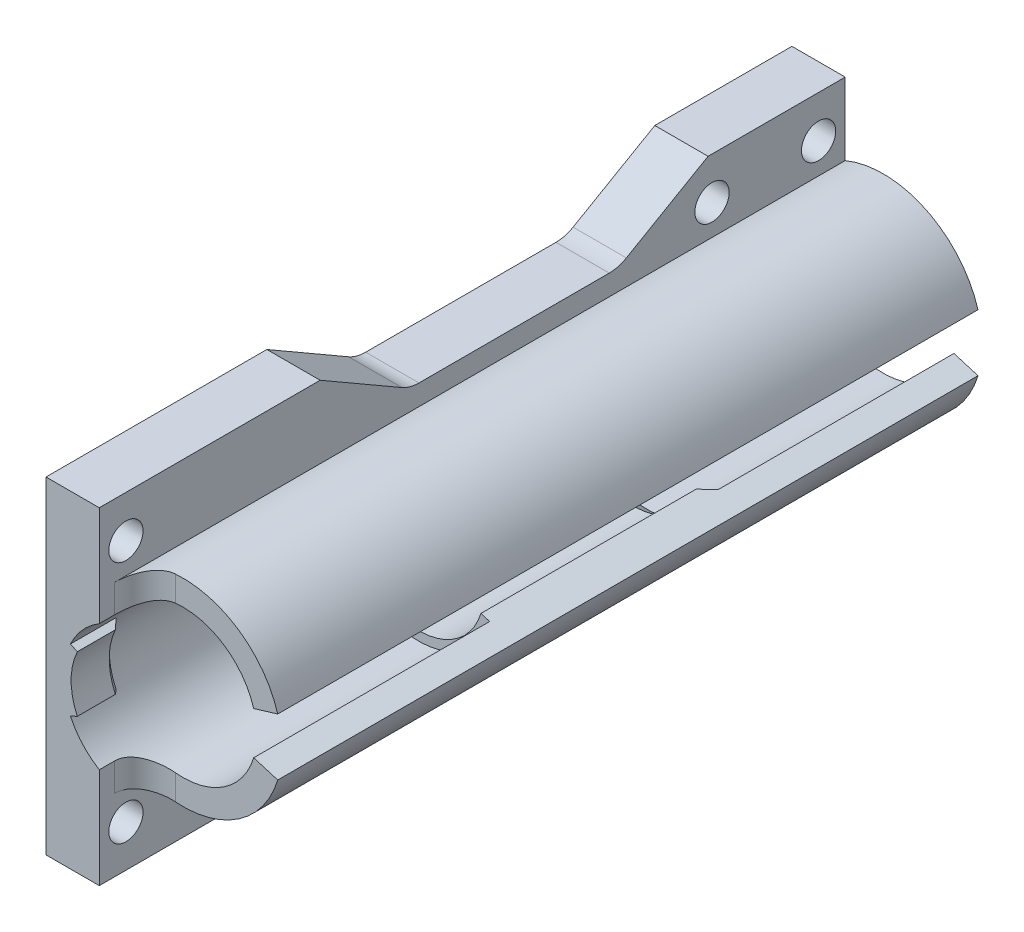
SolidWorks part; units mm, degrees
ref_plane "Front Plane" through (0, 0, 0) normal (0, 0, 1) x (1, 0, 0)
ref_plane "Top Plane" through (0, 0, 0) normal (0, 1, 0) x (1, 0, 0)
ref_plane "Right Plane" through (0, 0, 0) normal (1, 0, 0) x (0, 0, -1)
sketch "Sketch1" plane through (0, 0, 0) normal (0, 0, 1) x (1, 0, 0)
  line L0 (-5, -12) -> (-5, -21.5)
  line L1 (-12, 21.5) -> (-5, 21.5)
  line L2 (-12, 21.5) -> (-12, -21.5)
  line L3 (-12, -21.5) -> (-5, -21.5)
  line L4 (-5, 21.5) -> (-5, 12)
  line L5 (-12, 0) -> (0, 0) construction
  line L6 (9.2871, 2.8) -> (12.4466, 3.7526)
  line L7 (9.2871, -2.8) -> (12.4466, -3.7526)
  arc A0 (9.2871, 2.8) -> (9.2871, -2.8) centre (0, 0) ccw
  arc A1 (-5, -12) -> (12.4466, -3.7526) centre (0, 0) ccw
  arc A2 (12.4466, 3.7526) -> (-5, 12) centre (0, 0) ccw
  dimension "D4" = 19.4
  dimension "D5" = 13
  dimension "D1" = 7
  dimension "D2" = 43
  dimension "D3" = 12
  dimension "D6" = 5.6
extrude "Boss-Extrude1" add sketch "Sketch1" along normal blind 98
sketch "Sketch2" plane through (-12, 0, 0) normal (-1, 0, 0) x (0, 0, 1)
  line L0 (3.5, 16) -> (94.5, -16) construction
  line L1 (49, 0) -> (49, -21.5) construction
  line L2 (98, -21.5) -> (0, -21.5) construction
  line L3 (49, 0) -> (0, 0) construction
  circle A0 centre (3.5, 16) radius 2.25
  circle A1 centre (94.5, -16) radius 2.25
  circle A2 centre (94.5, 16) radius 2.25
  circle A3 centre (3.5, -16) radius 2.25
  circle A4 centre (17.5, 16) radius 2.25
  circle A5 centre (17.5, -16) radius 2.25
  dimension "D3" = 4.5
  dimension "D1" = 32
  dimension "D2" = 91
  dimension "D4" = 77
extrude "Cut-Extrude1" cut sketch "Sketch2" against normal through all
ref_plane "Plane1" through (0, 0, 0) normal (-1, 0, 0) x (0, 0, 1)
sketch "Sketch3" plane through (0, 0, 0) normal (-1, 0, 0) x (0, 0, 1)
  line L0 (0, 0) -> (50.5077, 0) construction
  line L1 (0, 21.5) -> (0, -21.5) construction
  line L2 (31, 9.7) -> (32.7138, 8.5)
  line L3 (32.7138, 8.5) -> (61, 8.5)
  line L4 (61, 8.5) -> (61, 9.7)
  line L5 (98, 9.7) -> (0, 9.7) construction
  line L7 (2, 9.7) -> (2, 5) construction
  line L8 (2, 5) -> (31, 5) construction
  line L9 (31, 5) -> (31, 9.7) construction
  line L10 (98, 21.5) -> (98, -21.5) construction
  line L11 (61, 9.7) -> (90, 9.7) construction
  line L12 (61, 9.7) -> (61, 5) construction
  line L13 (61, 5) -> (90, 5) construction
  line L14 (90, 9.7) -> (90, 5) construction
  line L15 (61, 9.7) -> (31, 9.7)
  dimension "D1" = 2
  dimension "D2" = 35
  dimension "D3" = 29
  dimension "D4" = 5
  dimension "D5" = 8
  dimension "D6" = 17
revolve "Revolve1" add sketch "Sketch3" angle 360 about L0
sketch "Sketch4" plane through (0, 0, 98) normal (0, 0, 1) x (1, 0, 0)
  line L0 (-12, -21.5) -> (-5, -21.5) construction
  line L1 (-5, 21.5) -> (14.6916, 21.5)
  line L2 (-5, 21.5) -> (-5, -21.5)
  line L3 (-5, -21.5) -> (14.6916, -21.5)
  line L4 (14.6916, 21.5) -> (14.6916, -21.5)
extrude "Cut-Extrude2" cut sketch "Sketch4" against normal blind 6
fillet "Fillet1" radius 4 1 edges at (-5, -10.156, 92)
sketch "Sketch5" plane through (0, 0, 61) normal (0, 0, 1) x (1, 0, 0)
  line L2 (9.2871, 2.8) -> (12.4466, 3.7526) construction
  line L3 (12.4466, -3.7526) -> (9.2871, -2.8) construction
  line L4 (8.1382, 2.4536) -> (9.2871, 2.8)
  line L5 (9.2871, -2.8) -> (8.1382, -2.4536)
  arc A0 (9.2871, -2.8) -> (9.2871, 2.8) centre (0, 0) ccw construction
  circle A1 centre (0, 0) radius 8.5 construction
  arc A2 (9.2871, -2.8) -> (9.2871, 2.8) centre (0, 0) ccw
  arc A3 (8.1382, -2.4536) -> (8.1382, 2.4536) centre (0, 0) ccw
extrude "Cut-Extrude3" cut sketch "Sketch5" against normal through all
sketch "Sketch6" plane through (-12, 0, 0) normal (-1, 0, 0) x (0, 0, 1)
  line L0 (28.75, 15.3029) -> (18.0163, 21.5)
  line L1 (98, 21.5) -> (0, 21.5) construction
  line L2 (18.0163, 21.5) -> (68.9837, 21.5)
  line L3 (68.9837, 21.5) -> (58.25, 15.3029)
  line L4 (31, 14.7) -> (56, 14.7)
  arc A0 (56, 14.7) -> (58.25, 15.3029) centre (56, 19.2) ccw
  arc A1 (28.75, 15.3029) -> (31, 14.7) centre (31, 19.2) ccw
  circle A2 centre (94.5, 16) radius 2.25 construction
  dimension "D1" = 38.5
  dimension "D3" = 9
  dimension "D2" = 25
  dimension "D4" = 19.2
  dimension "D5" = 30
  dimension "D6" = 30
extrude "Cut-Extrude4" cut sketch "Sketch6" against normal through all
mirror "Mirror1" about plane through (0, 0, 0) normal (0, 1, 0) of "Cut-Extrude4"
sketch "Sketch7" plane through (0, 0, 0) normal (0, 1, 0) x (1, 0, 0)
  line L0 (-9.7, -61) -> (-9.7, -98) construction
  line L1 (-9.7, -92) -> (-9.7, -98)
  line L2 (-9.7, -92) -> (-8.7, -93)
  line L3 (-8.7, -93) -> (-8.7, -98)
  line L4 (-8.5, -61) -> (8.1382, -61) construction
  line L5 (-8.7, -98) -> (-9.7, -98)
  line L6 (0, -97.1296) -> (0, -82.77) construction
  line L7 (0, -98) -> (0, -92) construction
  line L8 (0, -92) -> (0, 0) construction
  dimension "D1" = 45
  dimension "D2" = 1
  dimension "D3" = 31
revolve "Revolve2" add sketch "Sketch7" angle 25 about L6 other way angle 25
